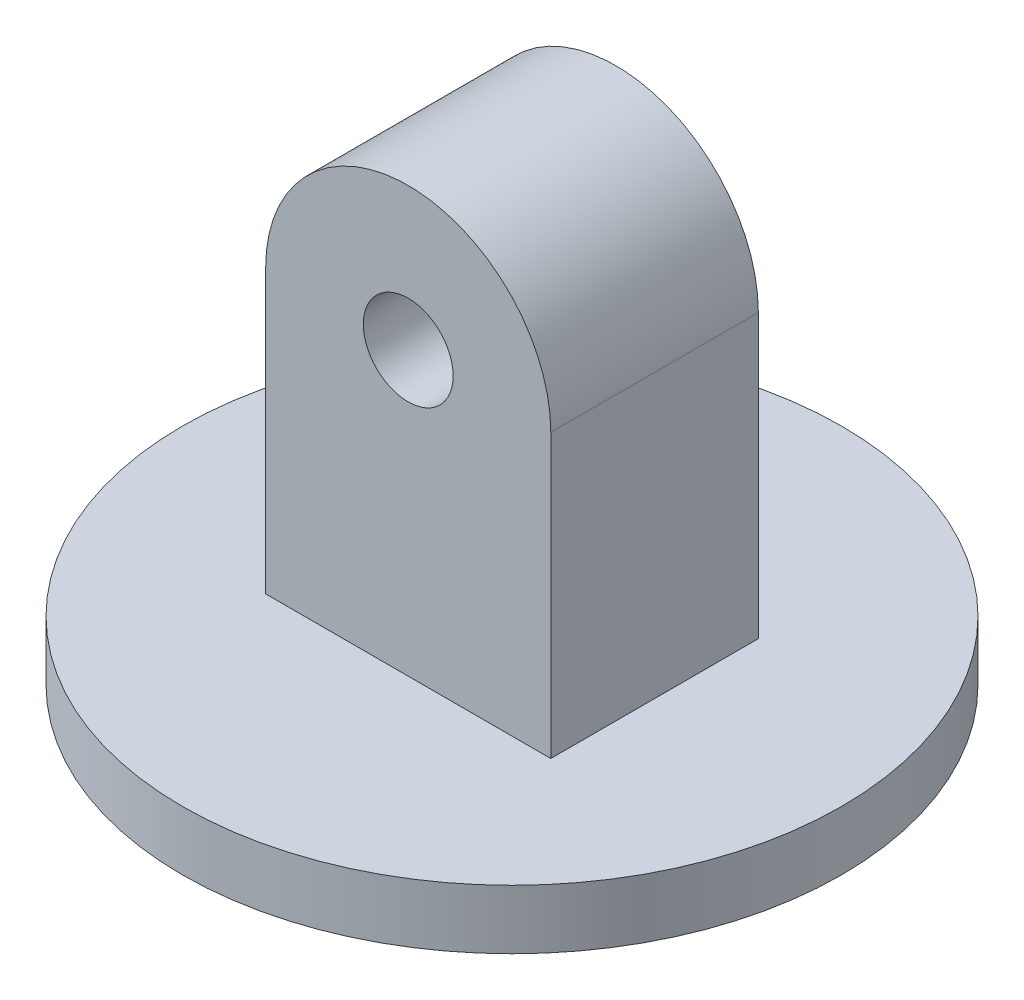
SolidWorks part; units mm, degrees
ref_plane "Front Plane" through (0, 0, 0) normal (0, 0, 1) x (1, 0, 0)
ref_plane "Top Plane" through (0, 0, 0) normal (0, 1, 0) x (1, 0, 0)
ref_plane "Right Plane" through (0, 0, 0) normal (1, 0, 0) x (0, 0, -1)
sketch "Sketch2" plane through (0, 0, 0) normal (0, 0, 1) x (1, 0, 0)
  line L0 (0, 0) -> (0, -19.05) construction
  line L1 (0, -19.05) -> (9.6161, -19.05)
  line L2 (9.6161, -19.05) -> (9.6161, 0)
  line L3 (0, -19.05) -> (-9.6161, -19.05)
  line L4 (-9.6161, -19.05) -> (-9.6161, 0)
  circle A0 centre (0, 0) radius 3.0287
  circle A1 centre (0, 0) radius 9.6161
  dimension "D1" = 19.05
extrude "Boss-Extrude1" add sketch "Sketch2" along normal blind 14
sketch "Sketch3" plane through (0, 0, 0) normal (1, 0, 0) x (0, 0, -1)
  line L0 (-7, -19.05) -> (15.225, -19.05)
  line L1 (-14, -19.05) -> (0, -19.05) construction
  line L2 (15.225, -19.05) -> (15.225, -23.05)
  line L3 (15.225, -23.05) -> (-7, -23.05)
  line L4 (-7, -23.05) -> (-7, -19.05) construction
  line L5 (-7, -19.05) -> (-7, -23.05)
  dimension "D1" = 4
  dimension "D2" = 22.225
revolve "Revolve1" add sketch "Sketch3" angle 360 about L4
sketch "Sketch4" plane through (0, -23.05, 0) normal (0, -1, 0) x (-1, 0, 0)
  circle A0 centre (0, -7) radius 22.225
  circle A1 centre (0, -7) radius 3.175
extrude "Cut-Extrude1" cut sketch "Sketch4" against normal blind 4 contours A1
